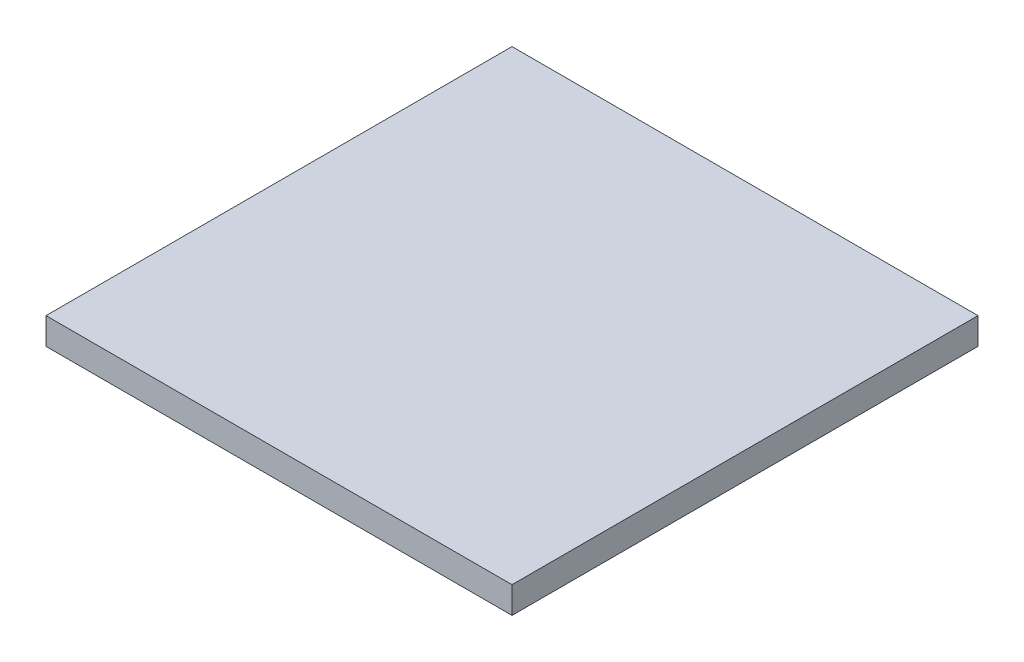
SolidWorks part; units mm, degrees
ref_plane "前视基准面" through (0, 0, 0) normal (0, 0, 1) x (1, 0, 0)
ref_plane "上视基准面" through (0, 0, 0) normal (0, 1, 0) x (1, 0, 0)
ref_plane "右视基准面" through (0, 0, 0) normal (1, 0, 0) x (0, 0, -1)
sketch "草图1" plane through (0, 0, 0) normal (0, 1, 0) x (1, 0, 0)
  line L1 (-17.5, 17.5) -> (17.5, 17.5)
  line L2 (-17.5, 17.5) -> (-17.5, -17.5)
  line L3 (-17.5, -17.5) -> (17.5, -17.5)
  line L4 (17.5, 17.5) -> (17.5, -17.5)
  line L5 (-17.5, 17.5) -> (17.5, -17.5) construction
  line L6 (-17.5, -17.5) -> (17.5, 17.5) construction
  point P0 (0, 0)
  dimension "D1" = 35
  dimension "D2" = 35
extrude "凸台-拉伸1" add sketch "草图1" along normal blind 2
